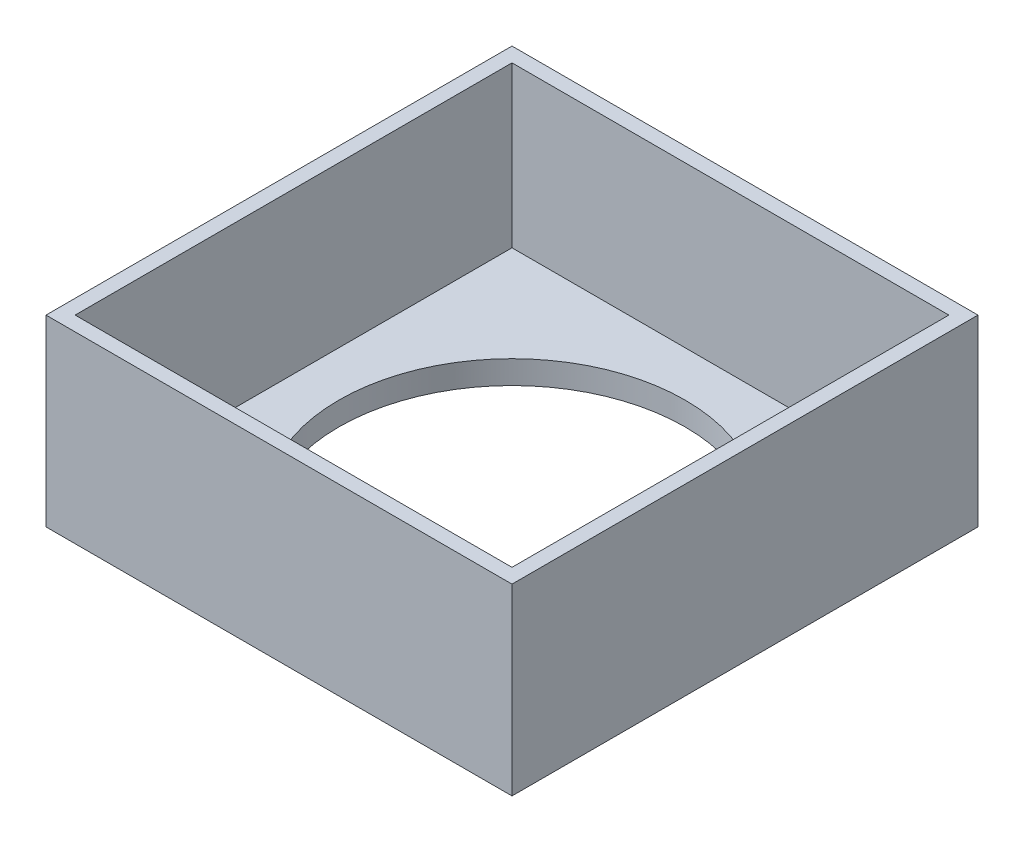
SolidWorks part; units mm, degrees
material "Balsa"
ref_plane "Front Plane" through (0, 0, 0) normal (0, 0, 1) x (1, 0, 0)
ref_plane "Top Plane" through (0, 0, 0) normal (0, 1, 0) x (1, 0, 0)
ref_plane "Right Plane" through (0, 0, 0) normal (1, 0, 0) x (0, 0, -1)
sketch "Sketch1" plane through (0, 0, 0) normal (0, 1, 0) x (1, 0, 0)
  line L5 (101.6, 101.6) -> (-101.6, 101.6)
  line L6 (101.6, 101.6) -> (101.6, -101.6)
  line L7 (101.6, -101.6) -> (-101.6, -101.6)
  line L8 (-101.6, 101.6) -> (-101.6, -101.6)
  line L9 (101.6, 101.6) -> (-101.6, -101.6) construction
  line L10 (101.6, -101.6) -> (-101.6, 101.6) construction
  point P1 (0, 0)
  dimension "D3" = 203.2
  dimension "D4" = 203.2
extrude "Boss-Extrude1" add sketch "Sketch1" along normal blind 80
sketch "Sketch3" plane through (0, 80, 0) normal (0, 1, 0) x (1, 0, 0)
  circle A0 centre (0, 0) radius 75.5
  dimension "D1" = 151
extrude "Cut-Extrude1" cut sketch "Sketch3" against normal blind 80
sketch "Sketch4" plane through (0, 80, 0) normal (0, 1, 0) x (1, 0, 0)
  line L0 (101.6, -101.6) -> (101.6, 101.6) construction
  line L1 (95.25, 95.25) -> (-95.25, 95.25)
  line L2 (95.25, 95.25) -> (95.25, -95.25)
  line L3 (95.25, -95.25) -> (-95.25, -95.25)
  line L4 (-95.25, 95.25) -> (-95.25, -95.25)
  line L5 (95.25, 95.25) -> (-95.25, -95.25) construction
  line L6 (95.25, -95.25) -> (-95.25, 95.25) construction
  line L7 (101.6, 101.6) -> (-101.6, 101.6) construction
  point P0 (0, 0)
  dimension "D1" = 6.35
  dimension "D2" = 6.35
extrude "Cut-Extrude2" cut sketch "Sketch4" against normal blind 69.85
